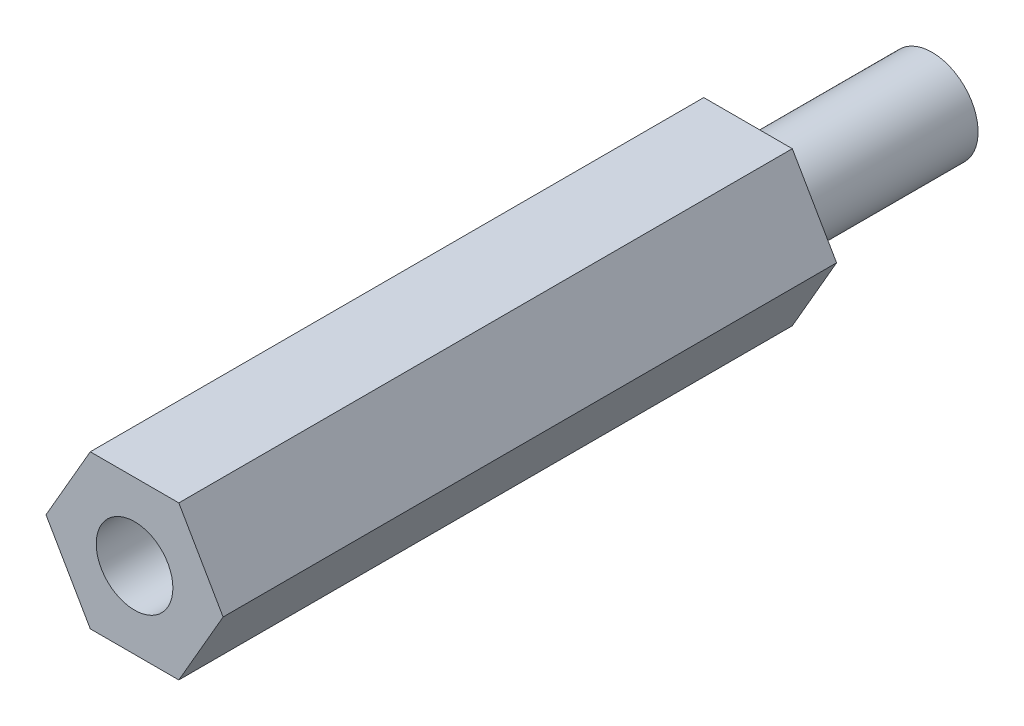
SolidWorks part; units mm, degrees
material "黃銅"
ref_plane "前基準面" through (0, 0, 0) normal (0, 0, 1) x (1, 0, 0)
ref_plane "上基準面" through (0, 0, 0) normal (0, 1, 0) x (1, 0, 0)
ref_plane "右基準面" through (0, 0, 0) normal (1, 0, 0) x (0, 0, -1)
sketch "草圖1" plane through (0, 0, 0) normal (0, 0, 1) x (1, 0, 0)
  line L1 (-1.4434, 2.5) -> (-2.8868, 0)
  line L2 (-2.8868, 0) -> (-1.4434, -2.5)
  line L3 (-1.4434, -2.5) -> (1.4434, -2.5)
  line L4 (1.4434, -2.5) -> (2.8868, 0)
  line L5 (2.8868, 0) -> (1.4434, 2.5)
  line L6 (1.4434, 2.5) -> (-1.4434, 2.5)
  circle A0 centre (0, 0) radius 2.5 construction
  dimension "D1" = 5
extrude "填料-伸長1" add sketch "草圖1" along normal blind 20
sketch "草圖4" plane through (0, 0, 0) normal (0, 0, -1) x (-1, 0, 0)
  circle A0 centre (0, 0) radius 1.5
  dimension "D1" = 3
extrude "填料-伸長2" add sketch "草圖4" along normal blind 6
hole_wizard "M3x0.5 螺紋孔1" positions "草圖2" profile "草圖3" tap size "M3x0.5" standard "Ansi Metric"
sketch "草圖2" plane through (0, 0, 20) normal (0, 0, 1) x (1, 0, 0)
  point P0 (0, 0)
sketch "草圖3" plane through (0, 0, 20) normal (1, 0, 0) x (0, -1, 0)
  line L0 (0, 0) -> (0, 8.2511)
  line L1 (0, 8.2511) -> (1.25, 7.5)
  line L2 (1.25, 7.5) -> (1.25, 0)
  line L5 (1.25, 0) -> (0, 0)
  line L10 (0, 8.2511) -> (-1.25, 7.5) construction
  line L11 (0, -6.35) -> (0, 107.95) construction
  dimension "螺孔鑽直徑" = 2.5
  dimension "螺孔鑽深度" = 7.5
  dimension "導頭角度" = 118
